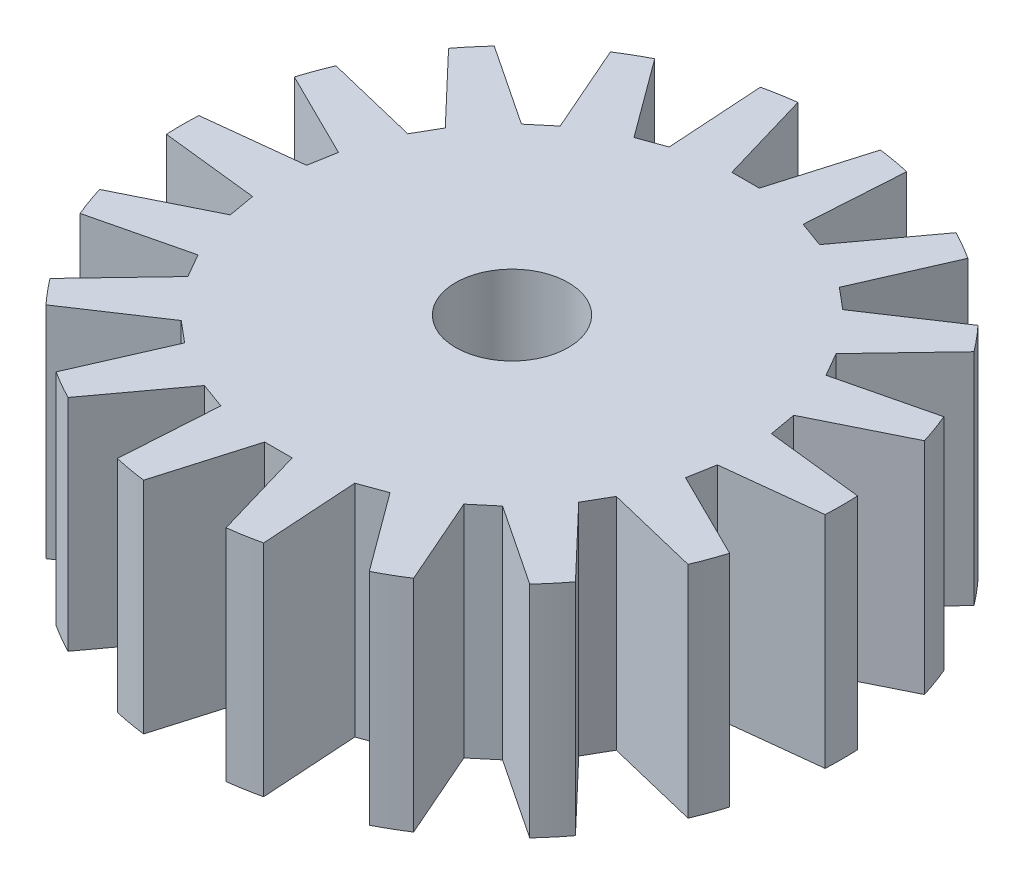
SolidWorks part; units mm, degrees
ref_plane "Front Plane" through (0, 0, 0) normal (0, 0, 1) x (1, 0, 0)
ref_plane "Top Plane" through (0, 0, 0) normal (0, 1, 0) x (1, 0, 0)
ref_plane "Right Plane" through (0, 0, 0) normal (1, 0, 0) x (0, 0, -1)
sketch "Sketch1" plane through (0, 0, 0) normal (0, 1, 0) x (1, 0, 0)
  circle A0 centre (0, 0) radius 12
  dimension "D1" = 24
extrude "Boss-Extrude1" add sketch "Sketch1" along normal blind 8
sketch "Sketch2" plane through (0, 8, 0) normal (0, 1, 0) x (1, 0, 0)
  circle A0 centre (0, 0) radius 2.05
  dimension "D1" = 4.1
extrude "Cut-Extrude1" cut sketch "Sketch2" against normal through all
sketch "Sketch3" plane through (0, 8, 0) normal (0, 1, 0) x (1, 0, 0)
  line L0 (0, 8.5) -> (0.5, 8.5)
  line L1 (0.5, 8.5) -> (1.5, 11.9059)
  line L2 (1.5, 11.9059) -> (1.5, 12.7411)
  line L3 (1.5, 12.7411) -> (-1.5, 12.7411)
  line L4 (-1.5, 12.7411) -> (-1.5, 11.9059)
  line L5 (-1.5, 11.9059) -> (-0.5, 8.5)
  line L6 (-0.5, 8.5) -> (0, 8.5)
  line L7 (0, 8.5) -> (0, 0) construction
  circle A0 centre (0, 0) radius 12 construction
  dimension "D1" = 0.5
  dimension "D2" = 0.5
  dimension "D3" = 1
  dimension "D4" = 1
  dimension "D5" = 8.5
extrude "Cut-Extrude2" cut sketch "Sketch3" against normal through all
pattern_circular "CirPattern1" count 18 every 20 about axis through (0, 0, 0) along (0, 1, 0) of "Cut-Extrude2"
